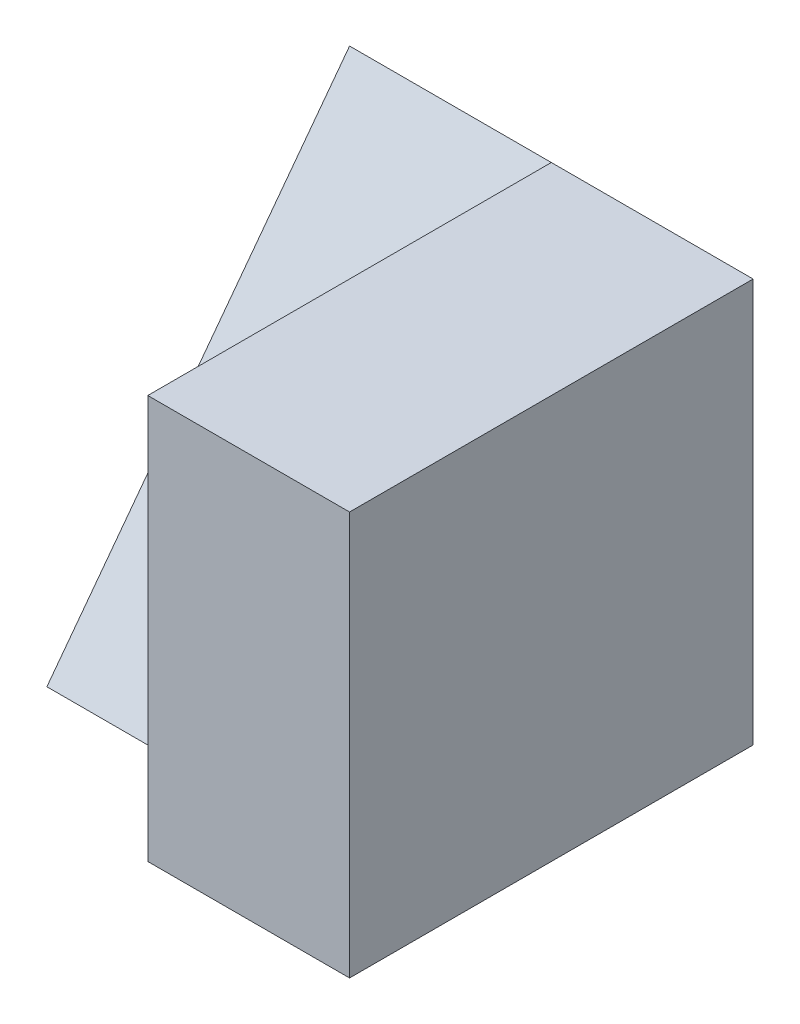
SolidWorks part; units mm, degrees
ref_plane "Front Plane" through (0, 0, 0) normal (0, 0, 1) x (1, 0, 0)
ref_plane "Top Plane" through (0, 0, 0) normal (0, 1, 0) x (1, 0, 0)
ref_plane "Right Plane" through (0, 0, 0) normal (1, 0, 0) x (0, 0, -1)
sketch "Sketch7" plane through (0, 0, 0) normal (0, 0, 1) x (1, 0, 0)
  line L1 (0, 0) -> (4, 0)
  line L2 (0, 0) -> (0, 4)
  line L3 (0, 4) -> (4, 4)
  line L4 (4, 0) -> (4, 4)
  dimension "D1" = 4
  dimension "D2" = 4
extrude "Boss-Extrude6" add sketch "Sketch7" along normal blind 4
sketch "Sketch8" plane through (0, 0, 0) normal (-1, 0, 0) x (0, 0, 1)
  line L0 (0, 4) -> (3, 0)
  line L1 (4, 0) -> (0, 0) construction
  line L2 (3, 0) -> (4, 0)
  line L3 (4, 0) -> (4, 4)
  line L4 (4, 4) -> (0, 4)
  dimension "D1" = 1
extrude "Cut-Extrude2" cut sketch "Sketch8" against normal blind 2
